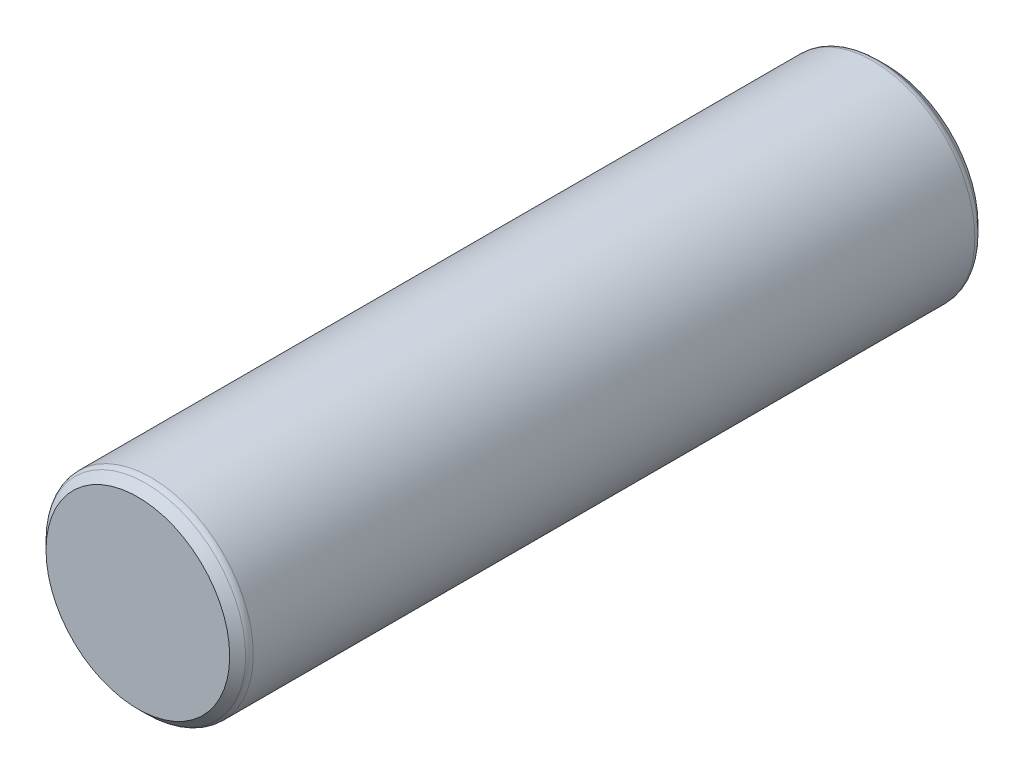
SolidWorks part; units mm, degrees
material "Plain Carbon Steel"
ref_plane "Front Plane" through (0, 0, 0) normal (0, 0, 1) x (1, 0, 0)
ref_plane "Top Plane" through (0, 0, 0) normal (0, 1, 0) x (1, 0, 0)
ref_plane "Right Plane" through (0, 0, 0) normal (1, 0, 0) x (0, 0, -1)
sketch "Sketch1" plane through (0, 0, 0) normal (0, 0, 1) x (1, 0, 0)
  line L0 (-7.5, 0) -> (7.5, 0) construction
  point P4 (0, 0)
  dimension "OD" = 15
sketch "Sketch2" plane through (0, 0, 0) normal (1, 0, 0) x (0, 0, -1)
  line L0 (27.5, 0) -> (-27.5, 0) construction
  line L1 (-27.5, 7.5) -> (-27.5, -7.5) construction
  line L2 (27.5, 7.5) -> (27.5, -7.5) construction
  point P0 (-10.25, 0)
  point P4 (0, 0)
  point P6 (10.25, 0)
  point P10 (27.5, 0)
  point P12 (-27.5, 0)
  dimension "Length" = 55
  dimension "D1" = 17.25
  dimension "D2" = 17.25
  dimension "D3" = 15
sketch "Sketch3" plane through (0, 0, 0) normal (0, 0, 1) x (1, 0, 0)
  circle A0 centre (0, 0) radius 7.5
extrude "Boss-Extrude1" add sketch "Sketch3" along normal mid plane 55
chamfer "Chamfer1" distance 0.75 angle 45 2 edges at (7.5, 0, 27.5) (7.5, 0, -27.5)
fillet "Fillet2" radius 0.5625 2 edges at (7.5, 0, 26.75) (7.5, 0, -26.75)
equation "\"D1@Boss-Extrude1\"=\"Length@Sketch2\""
equation "\"D1@Chamfer1\"=\"OD@Sketch1\"*.05"
equation "\"D1@Fillet2\"=\"D1@Chamfer1\"*.75"
equation "\"D3@Sketch2\"=\"OD@Sketch1\""
equation "\"D1@Sketch2\"=\"OD@Sketch1\"*1.15"
equation "\"D2@Sketch2\"=\"D1@Sketch2\""
